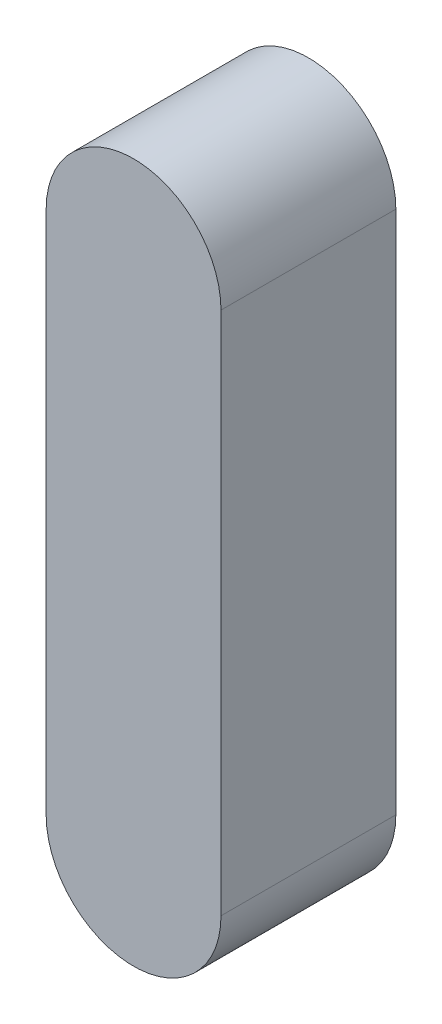
SolidWorks part; units mm, degrees
ref_plane "Přední rovina" through (0, 0, 0) normal (0, 0, 1) x (1, 0, 0)
ref_plane "Horní rovina" through (0, 0, 0) normal (0, 1, 0) x (1, 0, 0)
ref_plane "Pravá rovina" through (0, 0, 0) normal (1, 0, 0) x (0, 0, -1)
sketch "Skica1" plane through (0, 0, 0) normal (0, 0, 1) x (1, 0, 0)
  line L0 (0, 0) -> (0, 15) construction
  line L1 (-2.5, 0) -> (-2.5, 15)
  line L2 (2.5, 0) -> (2.5, 15)
  arc A0 (-2.5, 0) -> (2.5, 0) centre (0, 0) ccw
  arc A1 (2.5, 15) -> (-2.5, 15) centre (0, 15) ccw
  point P3 (0, 7.5)
  dimension "D2" = 20
  dimension "D1" = 5
extrude "Přidat vysunutím1" add sketch "Skica1" along normal blind 5
